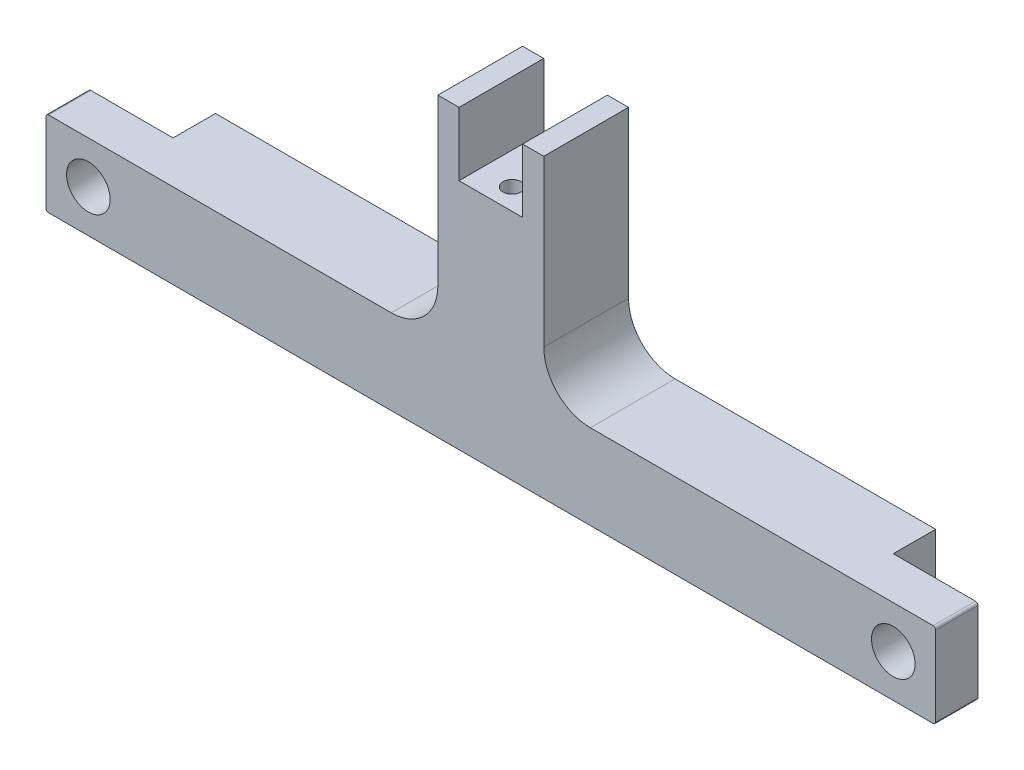
SolidWorks part; units mm, degrees
ref_plane "Front Plane" through (0, 0, 0) normal (0, 0, 1) x (1, 0, 0)
ref_plane "Top Plane" through (0, 0, 0) normal (0, 1, 0) x (1, 0, 0)
ref_plane "Right Plane" through (0, 0, 0) normal (1, 0, 0) x (0, 0, -1)
sketch "Sketch1" plane through (0, 0, 0) normal (0, 0, 1) x (1, 0, 0)
  line L0 (-7.9375, 13.335) -> (-7.9375, 38.1)
  line L1 (-66.294, -6.35) -> (66.294, -6.35)
  line L2 (-66.675, -5.969) -> (-66.675, 5.969)
  line L3 (-66.294, 6.35) -> (-14.9225, 6.35)
  line L4 (66.675, -5.969) -> (66.675, 5.969)
  line L5 (-66.675, -6.35) -> (66.675, 6.35) construction
  line L6 (-66.675, 6.35) -> (66.675, -6.35) construction
  line L7 (-7.9375, 38.1) -> (7.9375, 38.1)
  line L8 (7.9375, 38.1) -> (7.9375, 13.335)
  line L9 (14.9225, 6.35) -> (66.294, 6.35)
  circle A0 centre (-60.325, 0) radius 3.2639
  circle A1 centre (60.325, 0) radius 3.2639
  arc A2 (66.294, 6.35) -> (66.675, 5.969) centre (66.294, 5.969) cw
  arc A3 (66.294, -6.35) -> (66.675, -5.969) centre (66.294, -5.969) ccw
  arc A4 (-66.294, -6.35) -> (-66.675, -5.969) centre (-66.294, -5.969) cw
  arc A5 (-66.675, 5.969) -> (-66.294, 6.35) centre (-66.294, 5.969) cw
  arc A6 (7.9375, 13.335) -> (14.9225, 6.35) centre (14.9225, 13.335) ccw
  arc A7 (-7.9375, 13.335) -> (-14.9225, 6.35) centre (-14.9225, 13.335) cw
  point P0 (0, 0)
  point P28 (7.9375, 6.35)
  point P31 (-7.9375, 6.35)
  dimension "D3" = 6.5278
  dimension "D4" = 6.5278
  dimension "D7" = 0.381
  dimension "D11" = 6.985
  dimension "D1" = 12.7
  dimension "D2" = 133.35
  dimension "D5" = 60.325
  dimension "D6" = 60.325
  dimension "D8" = 31.75
  dimension "D9" = 15.875
  dimension "D10" = 7.9375
extrude "Boss-Extrude1" add sketch "Sketch1" along normal blind 12.7
sketch "Sketch2" plane through (0, 0, 0) normal (0, 0, -1) x (-1, 0, 0)
  line L0 (66.294, -6.35) -> (-66.294, -6.35) construction
  line L1 (-66.675, 6.35) -> (-53.975, 6.35)
  line L2 (-66.675, 6.35) -> (-66.675, -6.35)
  line L3 (-66.675, -6.35) -> (-53.975, -6.35)
  line L4 (-53.975, 6.35) -> (-53.975, -6.35)
  line L5 (14.9225, 6.35) -> (66.294, 6.35) construction
  line L6 (66.675, -6.35) -> (53.975, -6.35)
  line L7 (66.675, -6.35) -> (66.675, 6.35)
  line L8 (66.675, 6.35) -> (53.975, 6.35)
  line L9 (53.975, -6.35) -> (53.975, 6.35)
  line L10 (66.675, 5.969) -> (66.675, -5.969) construction
  circle A0 centre (-60.325, 0) radius 3.2639 construction
  dimension "D1" = 12.7
  dimension "D2" = 0
  dimension "D3" = 12.7
extrude "Cut-Extrude1" cut sketch "Sketch2" against normal blind 6.35
sketch "Sketch3" plane through (0, 38.1, 0) normal (0, 1, 0) x (1, 0, 0)
  line L0 (7.9375, -12.7) -> (-7.9375, -12.7) construction
  line L1 (-4.7625, -12.7) -> (4.7625, -12.7)
  line L2 (-4.7625, -12.7) -> (-4.7625, 0)
  line L3 (-4.7625, 0) -> (4.7625, 0)
  line L4 (4.7625, -12.7) -> (4.7625, 0)
  line L5 (7.9375, 0) -> (-7.9375, 0) construction
  dimension "D1" = 4.7625
  dimension "D2" = 4.7625
extrude "Cut-Extrude2" cut sketch "Sketch3" against normal blind 9.525
hole_wizard "#6-32 Tapped Hole1" positions "Sketch4" profile "Sketch5" tap size "#6-32" standard "ANSI Inch"
sketch "Sketch4" plane through (0, 28.575, 0) normal (0, 1, 0) x (1, 0, 0)
  line L0 (-4.7625, -12.7) -> (4.7625, -12.7) construction
  point P0 (0, -3.175)
  point P2 (0, -9.525)
  dimension "D1" = 6.35
  dimension "D2" = 3.175
sketch "Sketch5" plane through (0, 28.575, 3.175) normal (1, 0, 0) x (0, 0, 1)
  line L0 (0, 0) -> (0, 16.6877)
  line L1 (0, 16.6877) -> (1.3525, 15.875)
  line L2 (1.3525, 15.875) -> (1.3525, 0)
  line L5 (1.3525, 0) -> (0, 0)
  line L10 (0, 16.6877) -> (-1.3526, 15.875) construction
  line L11 (0, -6.35) -> (0, 107.95) construction
  dimension "Tap Drill Dia." = 2.7051
  dimension "Tap Drill Depth" = 15.875
  dimension "Drill Angle" = 118
